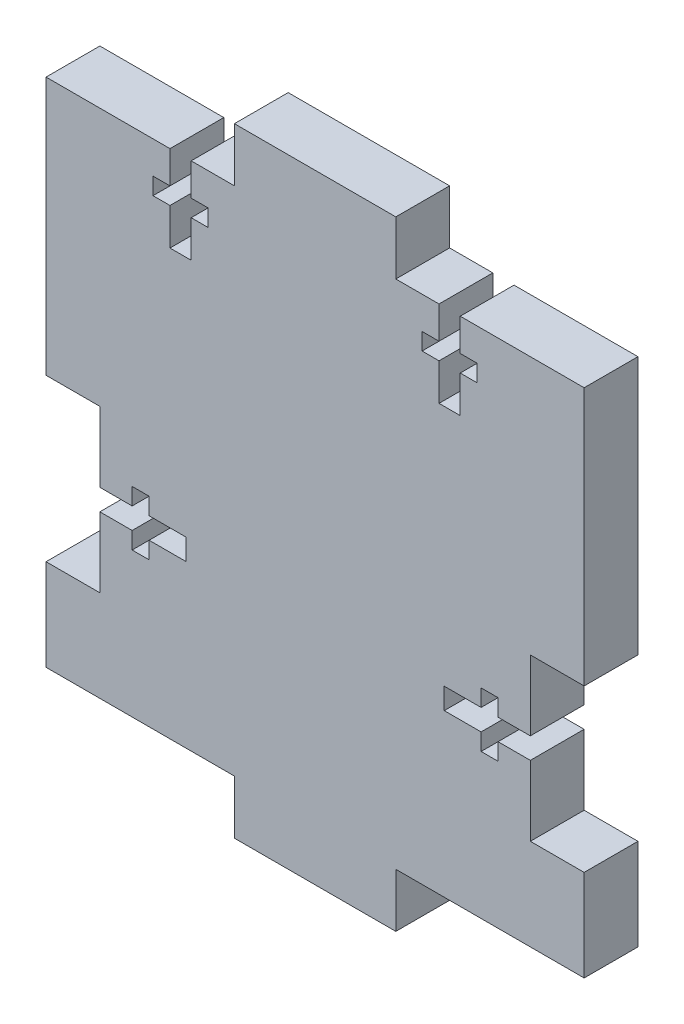
SolidWorks part; units mm, degrees
ref_plane "Front Plane" through (0, 0, 0) normal (0, 0, 1) x (1, 0, 0)
ref_plane "Top Plane" through (0, 0, 0) normal (0, 1, 0) x (1, 0, 0)
ref_plane "Right Plane" through (0, 0, 0) normal (1, 0, 0) x (0, 0, -1)
sketch "Sketch1" plane through (0, 0, 0) normal (0, 0, 1) x (1, 0, 0)
  line L0 (9.525, 66.675) -> (9.525, -6.35) construction
  line L1 (0, -6.35) -> (19.05, -6.35)
  line L2 (-15.875, 29.845) -> (-15.875, 21.57)
  line L3 (0, 66.675) -> (19.05, 66.675)
  line L4 (34.925, 29.845) -> (34.925, 21.57)
  line L5 (-22.225, 29.845) -> (-15.875, 29.845)
  line L6 (41.275, 29.845) -> (34.925, 29.845)
  line L7 (-15.875, 60.325) -> (-7.6, 60.325)
  line L8 (0, 66.675) -> (0, 60.325)
  line L9 (-22.225, 10.795) -> (-15.875, 10.795)
  line L10 (41.275, 10.795) -> (34.925, 10.795)
  line L11 (34.925, 60.325) -> (26.65, 60.325)
  line L12 (19.05, 66.675) -> (19.05, 60.325)
  line L13 (-15.875, 20.32) -> (-5.715, 20.32) construction
  line L14 (-15.875, 21.57) -> (-12.065, 21.57)
  line L15 (-15.875, 0) -> (0, 0)
  line L16 (0, -6.35) -> (0, 0)
  line L17 (34.925, 19.07) -> (31.115, 19.07)
  line L18 (-15.875, 19.07) -> (-12.065, 19.07)
  line L19 (34.925, 0) -> (19.05, 0)
  line L20 (19.05, -6.35) -> (19.05, 0)
  line L21 (-5.715, 21.57) -> (-5.715, 19.07)
  line L22 (-10.065, 21.57) -> (-5.715, 21.57)
  line L23 (-15.875, 60.325) -> (-22.225, 60.325)
  line L24 (-10.065, 19.07) -> (-5.715, 19.07)
  line L25 (-12.065, 21.57) -> (-12.065, 23.57)
  line L26 (-22.225, 60.325) -> (-22.225, 29.845)
  line L27 (-12.065, 23.57) -> (-10.065, 23.57)
  line L28 (-10.065, 21.57) -> (-10.065, 23.57)
  line L29 (-22.225, 10.795) -> (-22.225, 0)
  line L30 (-22.225, 0) -> (-15.875, 0)
  line L31 (-15.875, 19.07) -> (-15.875, 10.795)
  line L32 (34.925, 0) -> (41.275, 0)
  line L33 (-12.065, 19.07) -> (-12.065, 17.07)
  line L34 (-12.065, 17.07) -> (-10.065, 17.07)
  line L35 (41.275, 0) -> (41.275, 10.795)
  line L36 (41.275, 29.845) -> (41.275, 60.325)
  line L37 (41.275, 60.325) -> (34.925, 60.325)
  line L38 (-10.065, 19.07) -> (-10.065, 17.07)
  line L39 (31.115, 19.07) -> (31.115, 17.07)
  line L40 (31.115, 17.07) -> (29.115, 17.07)
  line L41 (29.115, 19.07) -> (29.115, 17.07)
  line L42 (29.115, 19.07) -> (24.765, 19.07)
  line L43 (34.925, 20.32) -> (24.765, 20.32) construction
  line L44 (24.765, 21.57) -> (24.765, 19.07)
  line L45 (29.115, 21.57) -> (24.765, 21.57)
  line L46 (29.115, 21.57) -> (29.115, 23.57)
  line L47 (31.115, 23.57) -> (29.115, 23.57)
  line L48 (31.115, 21.57) -> (31.115, 23.57)
  line L49 (34.925, 21.57) -> (31.115, 21.57)
  line L50 (34.925, 19.07) -> (34.925, 10.795)
  line L51 (-7.6, 54.515) -> (-7.6, 50.165)
  line L52 (24.15, 60.325) -> (19.05, 60.325)
  line L53 (-7.6, 60.325) -> (-7.6, 56.515)
  line L54 (-7.6, 50.165) -> (-5.1, 50.165)
  line L55 (-5.1, 60.325) -> (-5.1, 56.515)
  line L57 (24.15, 60.325) -> (24.15, 56.515)
  line L58 (24.15, 50.165) -> (26.65, 50.165)
  line L59 (26.65, 60.325) -> (26.65, 56.515)
  line L60 (-9.6, 56.515) -> (-7.6, 56.515)
  line L61 (-9.6, 56.515) -> (-9.6, 54.515)
  line L62 (-9.6, 54.515) -> (-7.6, 54.515)
  line L63 (-5.1, 54.515) -> (-5.1, 50.165)
  line L64 (-5.1, 56.515) -> (-3.1, 56.515)
  line L65 (24.15, 54.515) -> (24.15, 50.165)
  line L66 (-5.1, 54.515) -> (-3.1, 54.515)
  line L67 (-3.1, 56.515) -> (-3.1, 54.515)
  line L68 (22.15, 56.515) -> (24.15, 56.515)
  line L69 (22.15, 56.515) -> (22.15, 54.515)
  line L70 (22.15, 54.515) -> (24.15, 54.515)
  line L71 (26.65, 54.515) -> (26.65, 50.165)
  line L72 (26.65, 56.515) -> (28.65, 56.515)
  line L73 (-6.35, 60.325) -> (-6.35, 50.165) construction
  line L74 (26.65, 54.515) -> (28.65, 54.515)
  line L75 (28.65, 56.515) -> (28.65, 54.515)
  line L76 (25.4, 60.325) -> (25.4, 50.165) construction
  line L77 (-5.1, 60.325) -> (0, 60.325)
  dimension "D1" = 73.025
  dimension "D2" = 6.35
  dimension "D3" = 19.05
  dimension "D4" = 6.35
  dimension "D5" = 6.35
  dimension "D6" = 19.05
  dimension "D7" = 15.875
  dimension "D8" = 30.48
  dimension "D9" = 2.5
  dimension "D10" = 2
  dimension "D11" = 3.81
  dimension "D12" = 10.16
  dimension "D13" = 6.35
  dimension "D14" = 6.35
extrude "Boss-Extrude1" add sketch "Sketch1" along normal blind 6.35 contours L7 L53 L60 L61 L62 L51 L54 L63 L66 L67 L64 L55 L77 L8 L3 L12 L52 L57 L68 L69 L70 L65 L58 L71 L74 L75 L72 L59 L11 L37 L36 L6 L4 L49 L48 L47 L46 L45 L44 L42 L41 L40 L39 L17 L50 L10 L35 L32 L19 L20 L1 L16 L15 L30 L29 L9 L31 L18 L33 L34 L38 L24 L21 L22 L28 L27 L25 L14 L2 L5 L26 L23
